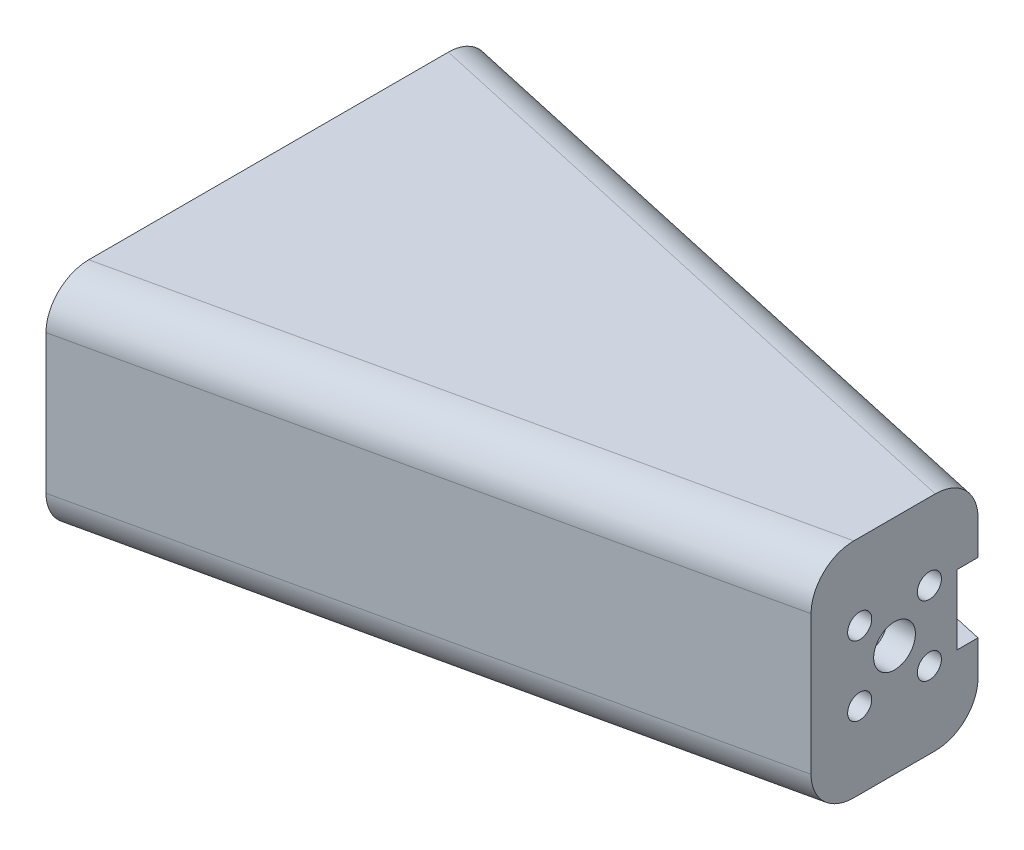
SolidWorks part; units mm, degrees
ref_plane "Front Plane" through (0, 0, 0) normal (0, 0, 1) x (1, 0, 0)
ref_plane "Top Plane" through (0, 0, 0) normal (0, 1, 0) x (1, 0, 0)
ref_plane "Right Plane" through (0, 0, 0) normal (1, 0, 0) x (0, 0, -1)
sketch "Sketch3" plane through (0, 0, 0) normal (0, 1, 0) x (1, 0, 0)
  line L0 (0, -20.32) -> (0, 20.32) construction
  line L1 (0, 20.32) -> (57.15, 7.62)
  line L2 (0, -20.32) -> (57.15, -7.62)
  line L3 (57.15, 7.62) -> (57.15, -7.62)
  line L4 (0, 17.718) -> (54.61, 5.5825)
  line L5 (54.61, 5.5825) -> (54.61, -5.5825)
  line L6 (54.61, -5.5825) -> (0, -17.718)
  line L7 (0, 20.32) -> (0, 17.718)
  line L8 (0, -17.718) -> (0, -20.32)
  point P4 (0, 0)
  dimension "D1" = 15.24
  dimension "D2" = 40.64
  dimension "D3" = 57.15
  dimension "D4" = 2.54
  dimension "D5" = 2.54
  dimension "D6" = 2.54
extrude "Boss-Extrude1" add sketch "Sketch3" along normal blind 17.78
sketch "Sketch4" plane through (57.15, 0, 0) normal (1, 0, 0) x (0, 0, -1)
  line L0 (7.62, 17.78) -> (-7.62, 0) construction
  line L1 (-7.62, 17.78) -> (7.62, 0) construction
  line L3 (-3.182, 5.708) -> (3.182, 5.708) construction
  line L4 (-3.182, 5.708) -> (-3.182, 12.072) construction
  line L5 (-3.182, 12.072) -> (3.182, 12.072) construction
  line L6 (3.182, 5.708) -> (3.182, 12.072) construction
  line L7 (-3.182, 5.708) -> (3.182, 12.072) construction
  line L8 (-3.182, 12.072) -> (3.182, 5.708) construction
  line L9 (5.715, 5.715) -> (9.525, 5.715)
  line L10 (5.715, 5.715) -> (5.715, 12.065)
  line L11 (5.715, 12.065) -> (9.525, 12.065)
  line L12 (9.525, 5.715) -> (9.525, 12.065)
  line L13 (5.715, 5.715) -> (9.525, 12.065) construction
  line L14 (5.715, 12.065) -> (9.525, 5.715) construction
  circle A0 centre (0, 8.89) radius 1.905
  circle A1 centre (-3.182, 12.072) radius 1.1
  circle A2 centre (3.182, 12.072) radius 1.1
  circle A3 centre (3.182, 5.708) radius 1.1
  circle A4 centre (-3.182, 5.708) radius 1.1
  point P18 (7.62, 8.89)
  point P23 (0, 0)
  dimension "D1" = 3.81
  dimension "D3" = 2.2
  dimension "D4" = 2.2
  dimension "D5" = 2.2
  dimension "D6" = 2.2
  dimension "D2" = 9
  dimension "D7" = 6.35
  dimension "D8" = 3.81
  dimension "D9" = 7.62
extrude "Cut-Extrude1" cut sketch "Sketch4" against normal blind 7.62
sketch "Sketch5" plane through (0, 17.78, 0) normal (0, 1, 0) x (1, 0, 0)
  line L0 (0, 20.32) -> (0, -20.32)
  line L1 (0, -20.32) -> (57.15, -7.62)
  line L2 (57.15, -7.62) -> (57.15, 7.62)
  line L3 (57.15, 7.62) -> (0, 20.32)
extrude "Boss-Extrude2" add sketch "Sketch5" along normal blind 1.27
sketch "Sketch6" plane through (0, 0, 0) normal (0, -1, 0) x (1, 0, 0)
  line L0 (0, 20.32) -> (0, -20.32)
  line L1 (0, -20.32) -> (57.15, -7.62)
  line L2 (57.15, -7.62) -> (57.15, 7.62)
  line L3 (57.15, 7.62) -> (0, 20.32)
extrude "Boss-Extrude3" add sketch "Sketch6" along normal blind 1.27
fillet "Fillet1" radius 3.81 4 edges at (28.575, -1.27, -13.97) (28.575, 19.05, -13.97) (28.575, 19.05, 13.97) (28.575, -1.27, 13.97)
